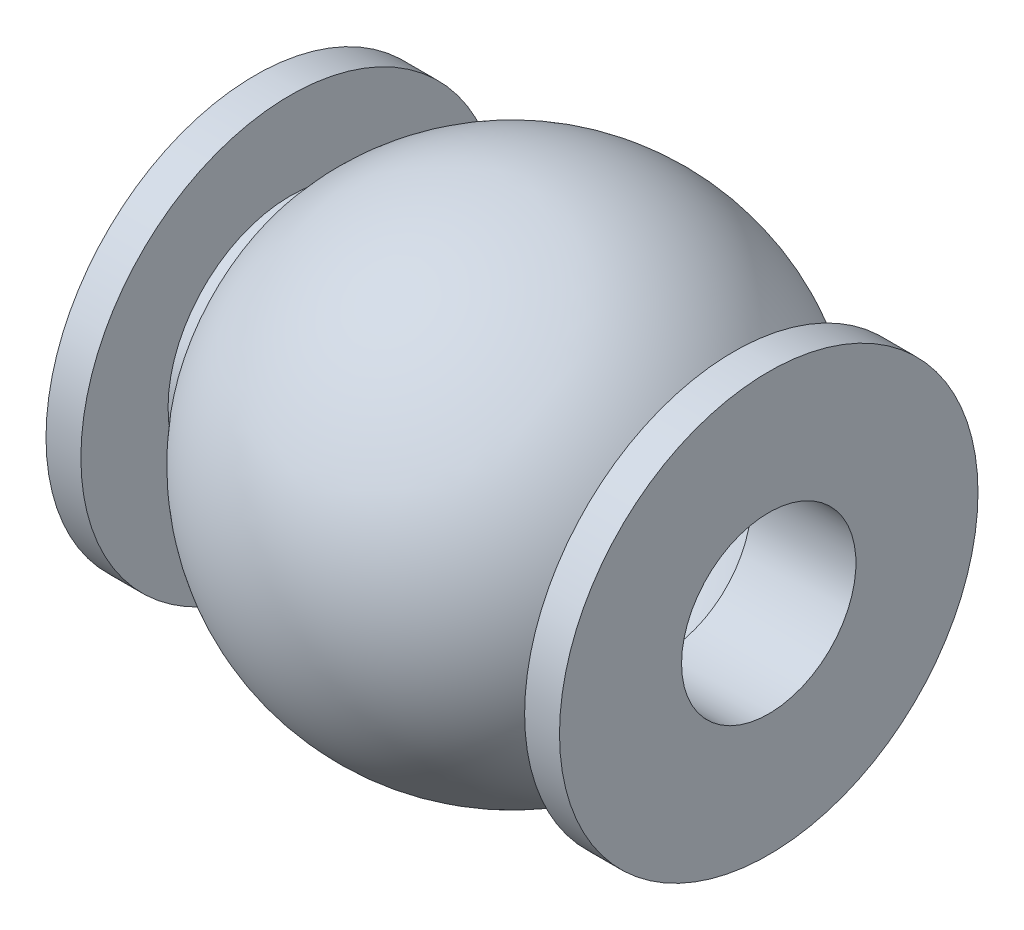
SolidWorks part; units mm, degrees
material "Резина"
ref_plane "Front" through (0, 0, 0) normal (0, 0, 1) x (1, 0, 0)
ref_plane "Top" through (0, 0, 0) normal (0, 1, 0) x (1, 0, 0)
ref_plane "Right" through (0, 0, 0) normal (1, 0, 0) x (0, 0, -1)
sketch "Эскиз1" plane through (0, 0, 0) normal (0, 0, 1) x (1, 0, 0)
  line L0 (0, 0) -> (0, 6)
  line L1 (0, 6) -> (1, 6)
  line L2 (1, 6) -> (1, 3.5)
  line L3 (1, 3.5) -> (2, 3.5)
  line L4 (0, 0) -> (3, 0)
  line L5 (7.3619, 0) -> (7.3619, 7) construction
  line L6 (12.7238, 3.5) -> (12.7238, 4.5)
  line L7 (13.7238, 3.5) -> (12.7238, 3.5)
  line L8 (13.7238, 6) -> (13.7238, 3.5)
  line L9 (14.7238, 6) -> (13.7238, 6)
  line L10 (2, 3.5) -> (2, 4.5)
  line L11 (14.7238, 0) -> (14.7238, 6)
  line L12 (11.7238, 0) -> (11.7238, 4.1199)
  line L13 (3, 0) -> (3, 4.1199)
  line L14 (3, 3.5) -> (3, 4.1199) construction
  line L15 (11.7238, 3.5) -> (11.7238, 4.1199) construction
  line L16 (11.7238, 0) -> (14.7238, 0)
  line L17 (3, 0) -> (11.7238, 0) construction
  arc A0 (12.7238, 4.5) -> (2, 4.5) centre (7.3619, 0) ccw
  arc A1 (11.7238, 4.1199) -> (3, 4.1199) centre (7.3619, 0) ccw
  dimension "D1" = 1
  dimension "D6" = 7
  dimension "D2" = 6
  dimension "D3" = 1
  dimension "D4" = 1
  dimension "D5" = 3.5
  dimension "D7" = 1
revolve "Повернуть1" add sketch "Эскиз1" angle 360 about L4
sketch "Эскиз2" plane through (0, 0, 0) normal (-1, 0, 0) x (0, 0, 1)
  circle A0 centre (0, 0) radius 2.5
  dimension "D1" = 5
extrude "Вырез-Вытянуть1" cut sketch "Эскиз2" against normal through all
